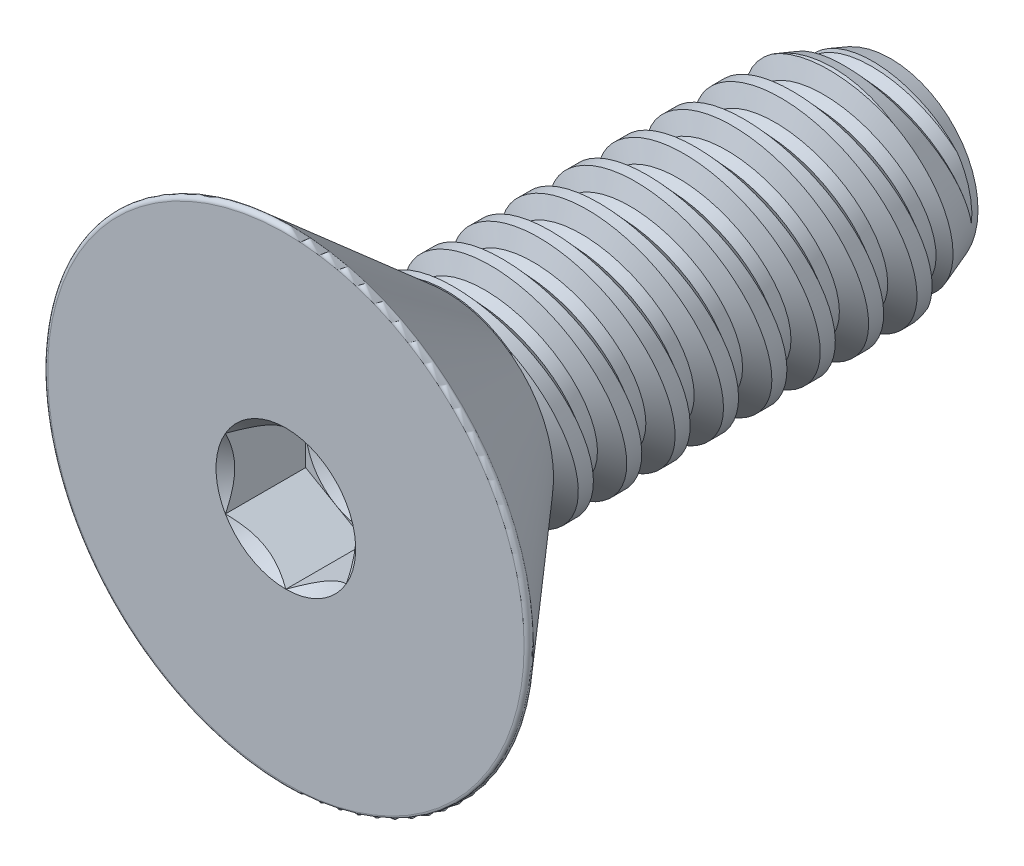
SolidWorks part; units mm, degrees
ref_plane "Front" through (0, 0, 0) normal (0, 0, 1) x (1, 0, 0)
ref_plane "Top" through (0, 0, 0) normal (0, 1, 0) x (1, 0, 0)
ref_plane "Right" through (0, 0, 0) normal (1, 0, 0) x (0, 0, -1)
sketch "Sketch1" plane through (0, 0, 0) normal (1, 0, 0) x (0, 0, -1)
  line L0 (0, 0) -> (-2.1082, 0) construction
  line L1 (0, 0) -> (5.8293, 0)
  line L2 (0, 0) -> (0, 1.4224)
  line L3 (0, 1.4224) -> (5.8293, 1.4224)
  line L4 (5.8293, 0) -> (5.8293, 1.4224)
  line L5 (0, -1.4224) -> (5.8293, -1.4224) construction
  dimension "D1" = 5.8293
  dimension "Thread Dia" = 2.8448
  dimension "Length" = 7.9375
  dimension "Head Height" = 2.1082
revolve "Revolve1" add sketch "Sketch1" angle 360 about L0
ref_plane "Plane1" through (0, 0, 2.1082) normal (0, 0, 1) x (1, 0, 0)
sketch "Sketch2" plane through (0, 0, 0) normal (1, 0, 0) x (0, 0, -1)
  line L0 (0, 1.4224) -> (0, -1.4224) construction
  line L1 (0, -1.4224) -> (0.635, -1.4224) construction
  line L2 (0.635, -1.4224) -> (0, 1.4224) construction
  line L3 (0, 1.4224) -> (0.0775, 1.4397) construction
  line L4 (0.0775, 1.4397) -> (0.6197, 1.5607)
  line L5 (0.6197, 1.5607) -> (0.501, 1.1821)
  line L6 (0.501, 1.1821) -> (0.346, 1.1475)
  line L7 (0.346, 1.1475) -> (0.0775, 1.4397)
  line L8 (0.4235, 1.1648) -> (0.3486, 1.5002) construction
  line L9 (0, -1.4224) -> (5.8293, -1.4224) construction
  line L10 (0, 1.4224) -> (5.8293, 1.4224) construction
  line L12 (0.366, 1.4224) -> (1.001, -1.4224) construction
  line L13 (0, -0.1526) -> (1.367, 0.1526) construction
  line L15 (0, 0) -> (0, 1.4224) construction
  point P19 (0.6835, 0)
  dimension "D1" = 60
  dimension "Thread Pitch" = 0.635
  dimension "D2" = 0.0794
  dimension "D3" = 0.1588
  dimension "D4" = 0.635
revolve "Cut-Revolve1" cut sketch "Sketch2" angle 360 about L13
sketch "Sketch3" plane through (0, 0, 0) normal (1, 0, 0) x (0, 0, -1)
  line L0 (5.8293, 1.1475) -> (5.0739, 1.4224)
  line L1 (5.0739, 1.4224) -> (5.8293, 1.4224)
  line L2 (5.8293, 1.4224) -> (5.8293, 1.1475)
  line L3 (0, 1.4224) -> (5.8293, 1.4224) construction
  line L4 (5.8293, 0) -> (5.8293, 1.4224) construction
  line L5 (5.0739, 0) -> (0, 0) construction
  line L6 (5.0739, 1.4224) -> (5.0739, -1.4224) construction
  line L7 (0, -1.4224) -> (5.8293, -1.4224) construction
  dimension "D1" = 20
  dimension "D2" = 2.8448
revolve "Cut-Revolve2" cut sketch "Sketch3" angle 360 about L5
pattern_linear "LPattern1" count 9 spacing 0.635 along (0, 0, 1)
pattern_linear "LPattern2" count 2 spacing 0.635 along (0, 0, 1)
sketch "Sketch4" plane through (0, 0, 0) normal (0, 0, 1) x (1, 0, 0)
  circle A0 centre (0, 0) radius 3.2385
  dimension "Head Dia" = 6.477
extrude "Extrude1" add sketch "Sketch4" along normal up to surface (2.1082 mm away)
sketch "Sketch9" plane through (0, 0, 0) normal (1, 0, 0) x (0, 0, -1)
  line L0 (-2.1082, 3.2385) -> (0, 1.4059)
  line L1 (0, 1.4059) -> (0, 3.2385)
  line L2 (0, 3.2385) -> (-2.1082, 3.2385)
  line L3 (0, 0) -> (-2.1082, 0) construction
  line L6 (-2.1082, -3.2385) -> (0, -1.4059) construction
  line L7 (0, -3.2385) -> (0, 3.2385) construction
  line L8 (-2.1082, 3.2385) -> (-2.1082, -3.2385) construction
  line L9 (0, 3.2385) -> (-2.1082, 3.2385) construction
  dimension "D1" = 82
revolve "Cut-Revolve3" cut sketch "Sketch9" angle 360 about L3
fillet "Fillet1" radius 0.0508
sketch "Sketch6" plane through (0, 0, 2.1082) normal (0, 0, 1) x (1, 0, 0)
  line L1 (0, -0.9165) -> (0.7937, -0.4583)
  line L2 (0.7937, -0.4583) -> (0.7937, 0.4583)
  line L3 (0.7937, 0.4583) -> (0, 0.9165)
  line L4 (0, 0.9165) -> (-0.7938, 0.4583)
  line L5 (-0.7938, 0.4583) -> (-0.7938, -0.4583)
  line L6 (-0.7938, -0.4583) -> (0, -0.9165)
  circle A0 centre (0, 0) radius 0.7938 construction
  dimension "Hex" = 1.5875
extrude "Cut-Extrude1" cut sketch "Sketch6" against normal blind 1.0541
sketch "Sketch7" plane through (0, 0, 2.1082) normal (0, 0, 1) x (1, 0, 0)
  circle A0 centre (0, 0) radius 0.9165
extrude "Cut-Extrude4" cut sketch "Sketch7" against normal blind 1.0541 draft 45
sketch "Sketch8" plane through (0, 0, 1.0541) normal (0, 0, 1) x (1, 0, 0)
  circle A0 centre (0, 0) radius 0.7938 construction
  circle A1 centre (0, 0) radius 0.7938
extrude "Cut-Extrude5" cut sketch "Sketch8" against normal blind 0.3514 draft 60
equation "\"D2@Sketch2\"=\"Thread Pitch@Sketch2\"/8"
equation "\"D3@Sketch2\"=\"Thread Pitch@Sketch2\"/4"
equation "\"D4@Sketch2\"=\"Thread Pitch@Sketch2\""
equation "\"D3@LPattern1\"=\"Thread Pitch@Sketch2\""
equation "\"D1@Cut-Extrude1\"=\"Head Height@Sketch1\"/2"
equation "\"D1@Cut-Extrude4\"=\"D1@Cut-Extrude1\""
equation "\"D1@Cut-Extrude5\"=\"D1@Cut-Extrude1\"/3"
equation "\"D1@LPattern1\"=\"D1@Sketch1\"/\"Thread Pitch@Sketch2\""
equation "\"D3@LPattern2\"=\"Thread Pitch@Sketch2\""
